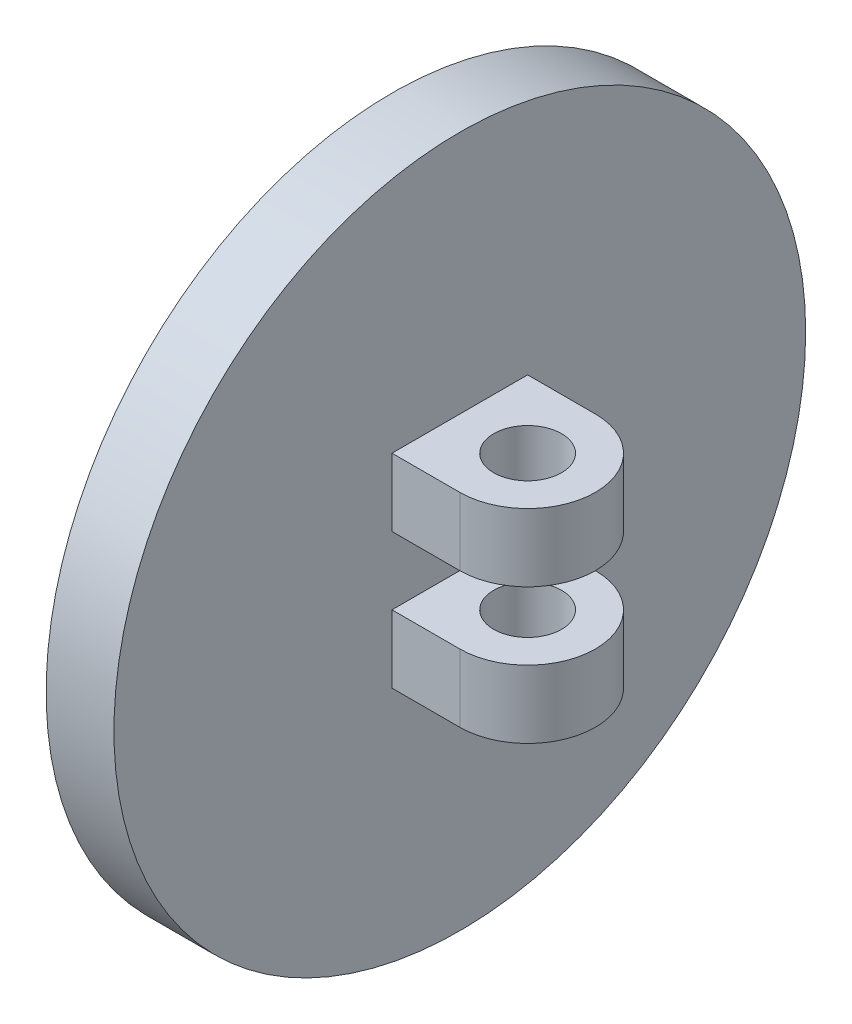
SolidWorks part; units mm, degrees
ref_plane "Front Plane" through (0, 0, 0) normal (0, 0, 1) x (1, 0, 0)
ref_plane "Top Plane" through (0, 0, 0) normal (0, 1, 0) x (1, 0, 0)
ref_plane "Right Plane" through (0, 0, 0) normal (1, 0, 0) x (0, 0, -1)
sketch "Sketch1" plane through (0, 0, 0) normal (1, 0, 0) x (0, 0, -1)
  circle A0 centre (0, 0) radius 5.1
  dimension "D1" = 10.2
extrude "Boss-Extrude1" add sketch "Sketch1" along normal blind 1
sketch "Sketch2" plane through (0, 0, 0) normal (0, 1, 0) x (1, 0, 0)
  line L0 (1, 1) -> (2, 1)
  line L1 (1, -5.1) -> (1, 5.1) construction
  line L2 (2, -1) -> (1, -1)
  line L3 (1, 1) -> (1, -1)
  arc A0 (2, 1) -> (2, -1) centre (2, 0) cw
  circle A1 centre (2, 0) radius 0.5
  dimension "D2" = 1
  dimension "D3" = 1
  dimension "D1" = 2
extrude "Boss-Extrude2" add sketch "Sketch2" along normal blind 1 from offset 0.5
mirror "Mirror1" about plane through (0, 0, 0) normal (0, 1, 0) of "Boss-Extrude2"
